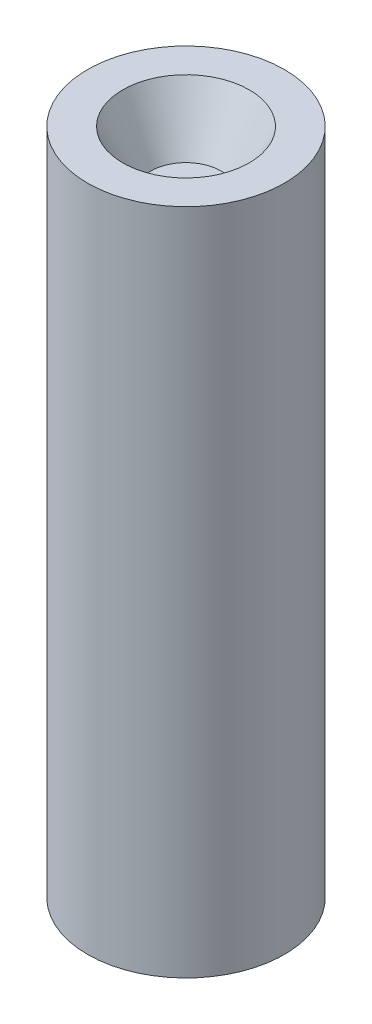
SolidWorks part; units mm, degrees
ref_plane "Front Plane" through (0, 0, 0) normal (0, 0, 1) x (1, 0, 0)
ref_plane "Top Plane" through (0, 0, 0) normal (0, 1, 0) x (1, 0, 0)
ref_plane "Right Plane" through (0, 0, 0) normal (1, 0, 0) x (0, 0, -1)
sketch "Sketch1" plane through (0, 0, 0) normal (0, 0, 1) x (1, 0, 0)
  line L1 (0, 0) -> (1.4, 0)
  line L2 (0, 0) -> (0, 8.7)
  line L4 (1.4, 0) -> (1.4, 9.5)
  line L7 (1.4, 9.5) -> (0.9, 9.5)
  line L8 (0.9, 9.5) -> (0.5, 8.7)
  line L9 (0.5, 8.7) -> (0, 8.7)
  dimension "D1" = 9.5
  dimension "D2" = 1.4
  dimension "D3" = 8.7
  dimension "D4" = 0.5
  dimension "D5" = 0.5
revolve "Revolve1" add sketch "Sketch1" angle 360 about L2
